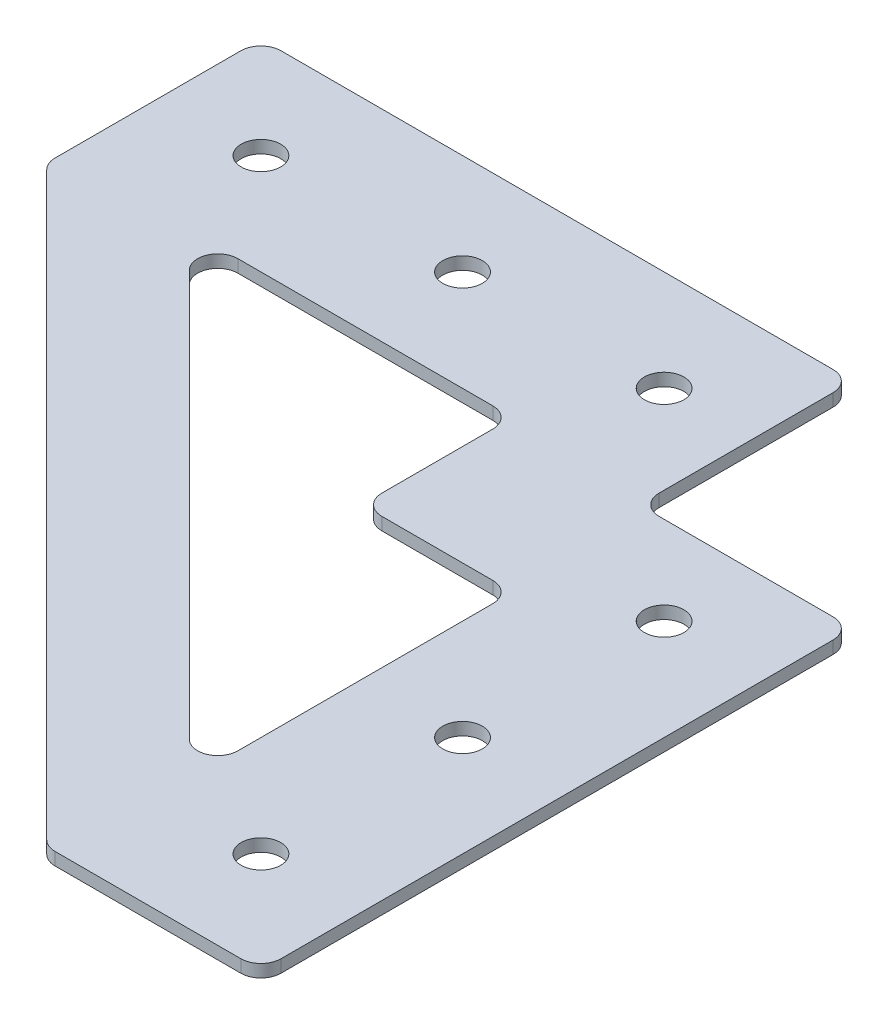
SolidWorks part; units mm, degrees
material "6061-T6 (SS)"
ref_plane "Front Plane" through (0, 0, 0) normal (0, 0, 1) x (1, 0, 0)
ref_plane "Top Plane" through (0, 0, 0) normal (0, 1, 0) x (1, 0, 0)
ref_plane "Right Plane" through (0, 0, 0) normal (1, 0, 0) x (0, 0, -1)
sketch "Sketch1" plane through (0, 0, 0) normal (0, 1, 0) x (1, 0, 0)
  line L0 (0, -26.9875) -> (-26.9875, -26.9875)
  line L2 (0, -26.9875) -> (0, -101.6)
  line L5 (-26.9875, 0) -> (-101.6, 0)
  line L9 (-26.9875, 0) -> (-26.9875, -26.9875)
  line L10 (-101.6, 0) -> (-101.6, -26.9875)
  line L11 (0, -101.6) -> (-26.9875, -101.6)
  line L12 (-101.6, -26.9875) -> (-26.9875, -101.6)
  line L13 (-85.227, -25.4) -> (-25.4, -85.227)
  line L14 (-26.9875, -26.9875) -> (-26.9875, -101.6) construction
  line L17 (-25.4, -44.45) -> (-44.45, -44.45)
  line L18 (-44.45, -25.4) -> (-44.45, -44.45)
  line L19 (-26.9875, -26.9875) -> (-101.6, -26.9875) construction
  line L20 (0, 0) -> (0, -101.6) construction
  line L21 (0, 0) -> (-101.6, 0) construction
  line L22 (-25.4, -44.45) -> (-25.4, -85.227)
  line L23 (-44.45, -25.4) -> (-85.227, -25.4)
  dimension "D1" = 101.6
  dimension "D2" = 25.4
  dimension "D3" = 12.7
  dimension "D5" = 44.45
  dimension "D6" = 25.4
  dimension "D7" = 26.9875
extrude "Boss-Extrude1" add sketch "Sketch1" along normal blind 1.5875
fillet "Fillet1" radius 2.54 12 edges at (-85.227, 0.7937, 25.4) (-25.4, 0.7937, 85.227) (-25.4, 0.7937, 44.45) (-44.45, 0.7937, 44.45) (-44.45, 0.7937, 25.4) (-26.9875, 0.7937, 26.9875) (0, 0.7937, 26.9875) (-26.9875, 0.7937, 101.6) (-101.6, 0.7937, 26.9875) (-101.6, 0.7937, 0) (-26.9875, 0.7937, 0) (0, 0.7937, 101.6)
sketch "Sketch2" plane through (0, 1.5875, 0) normal (0, 1, 0) x (1, 0, 0)
  line L0 (-101.6, -2.54) -> (-101.6, -25.9354) construction
  line L1 (-29.5275, 0) -> (-99.06, 0) construction
  line L2 (-25.9354, -101.6) -> (-2.54, -101.6) construction
  line L3 (0, -99.06) -> (0, -29.5275) construction
  circle A0 centre (-88.9, -12.7) radius 2.4892
  circle A1 centre (-12.7, -88.9) radius 2.4892
  dimension "D1" = 4.9784
  dimension "D5" = 12.7
  dimension "D2" = 12.7
  dimension "D3" = 12.7
  dimension "D4" = 12.7
extrude "Cut-Extrude1" cut sketch "Sketch2" against normal through all
pattern_linear "LPattern1" count 3 spacing 25.4 along (1, 0, 0) of "Cut-Extrude1"
pattern_linear "LPattern2" count 3 spacing 25.4 along (0, 0, -1) of "Cut-Extrude1"
